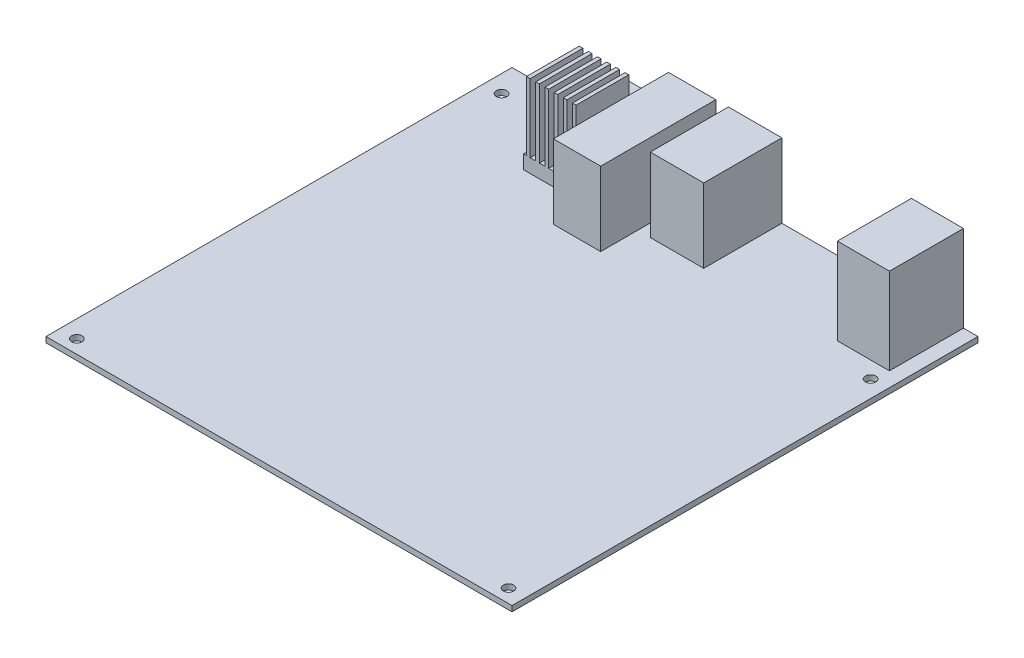
SolidWorks part; units mm, degrees
ref_plane "Front Plane" through (0, 0, 0) normal (0, 0, 1) x (1, 0, 0)
ref_plane "Top Plane" through (0, 0, 0) normal (0, 1, 0) x (1, 0, 0)
ref_plane "Right Plane" through (0, 0, 0) normal (1, 0, 0) x (0, 0, -1)
sketch "Sketch1" plane through (0, 0, 0) normal (0, 1, 0) x (1, 0, 0)
  line L1 (-85, 85) -> (85, 85)
  line L2 (-85, 85) -> (-85, -85)
  line L3 (-85, -85) -> (85, -85)
  line L4 (85, 85) -> (85, -85)
  line L5 (-85, 85) -> (85, -85) construction
  line L6 (-85, -85) -> (85, 85) construction
  point P0 (0, 0)
  dimension "D1" = 170
extrude "Boss-Extrude1" add sketch "Sketch1" along normal blind 2
sketch "Sketch2" plane through (0, 2, 0) normal (0, 1, 0) x (1, 0, 0)
  line L0 (-85, 85) -> (-85, -85) construction
  line L1 (85, 85) -> (-85, 85) construction
  point P0 (-78.65, 74.84)
  point P1 (78.83, 51.98)
  point P2 (-78.65, -80.1)
  point P3 (78.83, -80.1)
  dimension "D1" = 6.35
  dimension "D2" = 10.16
  dimension "D3" = 154.94
  dimension "D4" = 157.48
  dimension "D5" = 22.86
hole_wizard "#6 Clearance Hole1" positions "3DSketch1" profile "Sketch3" hole size "#6" standard "ANSI Inch" end condition through all
sketch3d "3DSketch1"
  point P0 (-78.65, 2, -74.84)
  point P3 (-78.65, 2, 80.1)
  point P6 (78.83, 2, 80.1)
  point P9 (78.83, 2, -51.98)
sketch "Sketch3" plane through (-78.65, 2, -74.84) normal (1, 0, 0) x (0, 0, 1)
  line L0 (0, 0) -> (0, 2)
  line L1 (0, 2) -> (1.8986, 2)
  line L2 (1.8986, 2) -> (1.8986, 0)
  line L5 (1.8986, 0) -> (0, 0)
  line L11 (0, -6.35) -> (0, 107.95) construction
  dimension "Thru Hole Dia." = 3.7973
  dimension "Thru Hole Depth" = 2
sketch "Sketch5" plane through (0, 2, 0) normal (0, 1, 0) x (1, 0, 0)
  line L0 (85, 85) -> (-85, 85) construction
  line L1 (60.7, 58) -> (79.7, 58)
  line L2 (60.7, 58) -> (60.7, 85)
  line L3 (60.7, 85) -> (79.7, 85)
  line L4 (79.7, 58) -> (79.7, 85)
  line L5 (60.7, 58) -> (79.7, 85) construction
  line L6 (60.7, 85) -> (79.7, 58) construction
  line L7 (85, -85) -> (85, 85) construction
  point P0 (70.2, 71.5)
  point P9 (70.2, 58)
  point P10 (70.2, 85)
  dimension "D1" = 19
  dimension "D2" = 5.3
  dimension "D3" = 27
extrude "Boss-Extrude2" add sketch "Sketch5" along normal blind 31.5
sketch "Sketch6" plane through (0, 2, 0) normal (0, 1, 0) x (1, 0, 0)
  line L0 (60.7, 85) -> (-85, 85) construction
  line L1 (-6.05, 56.5) -> (13.45, 56.5)
  line L2 (-6.05, 56.5) -> (-6.05, 85)
  line L3 (-6.05, 85) -> (13.45, 85)
  line L4 (13.45, 56.5) -> (13.45, 85)
  line L5 (-6.05, 56.5) -> (13.45, 85) construction
  line L6 (-6.05, 85) -> (13.45, 56.5) construction
  line L7 (60.7, 85) -> (60.7, 58) construction
  line L9 (-27.9, 43) -> (-10.65, 43)
  line L10 (-27.9, 43) -> (-27.9, 85)
  line L11 (-27.9, 85) -> (-10.65, 85)
  line L12 (-10.65, 43) -> (-10.65, 85)
  line L13 (-27.9, 43) -> (-10.65, 85) construction
  line L14 (-27.9, 85) -> (-10.65, 43) construction
  point P0 (3.7, 70.75)
  point P9 (3.7, 56.5)
  point P10 (-19.275, 64)
  dimension "D1" = 47.25
  dimension "D2" = 19.5
  dimension "D3" = 28.5
  dimension "D4" = 4.6
  dimension "D5" = 17.25
  dimension "D6" = 42
extrude "Boss-Extrude3" add sketch "Sketch6" along normal blind 27
sketch "Sketch7" plane through (0, 2, 0) normal (0, 1, 0) x (1, 0, 0)
  line L0 (-27.9, 85) -> (-27.9, 43) construction
  line L1 (-50.6, 74) -> (-31.4, 74)
  line L2 (-50.6, 74) -> (-50.6, 54.8)
  line L3 (-50.6, 54.8) -> (-31.4, 54.8)
  line L4 (-31.4, 74) -> (-31.4, 54.8)
  line L5 (-50.6, 74) -> (-31.4, 54.8) construction
  line L6 (-50.6, 54.8) -> (-31.4, 74) construction
  line L7 (-27.9, 85) -> (-85, 85) construction
  point P0 (-41, 64.4)
  point P7 (-41, 74)
  dimension "D1" = 19.2
  dimension "D2" = 3.5
  dimension "D3" = 11
extrude "Boss-Extrude4" add sketch "Sketch7" along normal blind 30
sketch "Sketch8" plane through (0, 0, -74) normal (0, 0, -1) x (-1, 0, 0)
  line L0 (31.4, 32) -> (50.6, 32) construction
  line L1 (31.4, 32) -> (32.75, 32)
  line L2 (31.4, 32) -> (31.4, 7)
  line L3 (31.4, 7) -> (32.75, 7)
  line L4 (32.75, 32) -> (32.75, 7)
  line L5 (34.75, 32) -> (34.75, 7)
  line L6 (34.75, 32) -> (36.1, 32)
  line L7 (36.1, 32) -> (36.1, 7)
  line L8 (34.75, 7) -> (36.1, 7)
  line L9 (38.1, 32) -> (38.1, 7)
  line L10 (38.1, 32) -> (39.45, 32)
  line L11 (39.45, 32) -> (39.45, 7)
  line L12 (38.1, 7) -> (39.45, 7)
  line L13 (41.45, 32) -> (41.45, 7)
  line L14 (41.45, 32) -> (42.8, 32)
  line L15 (42.8, 32) -> (42.8, 7)
  line L16 (41.45, 7) -> (42.8, 7)
  line L17 (44.8, 32) -> (44.8, 7)
  line L18 (44.8, 32) -> (46.15, 32)
  line L19 (46.15, 32) -> (46.15, 7)
  line L20 (44.8, 7) -> (46.15, 7)
  line L21 (48.15, 32) -> (48.15, 7)
  line L22 (48.15, 32) -> (49.5, 32)
  line L23 (49.5, 32) -> (49.5, 7)
  line L24 (48.15, 7) -> (49.5, 7)
  line L25 (31.4, 7) -> (50.6, 7)
  line L29 (31.4, 2) -> (50.6, 2)
  line L30 (50.6, 2) -> (50.6, 32)
  line L31 (50.6, 32) -> (31.4, 32)
  line L32 (31.4, 32) -> (31.4, 2)
  line L33 (31.4, 2) -> (50.6, 2)
  line L34 (50.6, 2) -> (50.6, 32)
  line L35 (50.6, 32) -> (31.4, 32)
  line L36 (31.4, 32) -> (31.4, 2)
  point P5 (32.075, 7)
  line M11 (50.6, 2) -> (50.6, 32)
  line M12 (50.6, 32) -> (31.4, 32)
  dimension "D1" = 1.35
  dimension "D2" = 25
  dimension "D5" = 2
  dimension "D4" = 0
  dimension "D3" = 6
extrude "Cut-Extrude1" cut sketch "Sketch8" against normal through all contours L4 L25 L5 M12 | L7 L25 L9 M12 | L11 L25 L13 M12 | L15 L25 L17 M12 | L19 L25 L21 M12 | L23 L25 M11 M12 | L36 L33 L34 L35
sketch "Sketch9" plane through (0, 0, -85) normal (0, 0, -1) x (-1, 0, 0)
  line L0 (27.9, 2) -> (85, 2) construction
  line L1 (32.4, 2) -> (63.4, 2)
  line L2 (32.4, 2) -> (32.4, 13)
  line L3 (32.4, 13) -> (63.4, 13)
  line L4 (63.4, 2) -> (63.4, 13)
  line L5 (27.9, 29) -> (27.9, 2) construction
  dimension "D1" = 4.5
  dimension "D2" = 11
  dimension "D3" = 31
extrude "Boss-Extrude5" add sketch "Sketch9" along normal blind 6 and the other way blind 4.2
